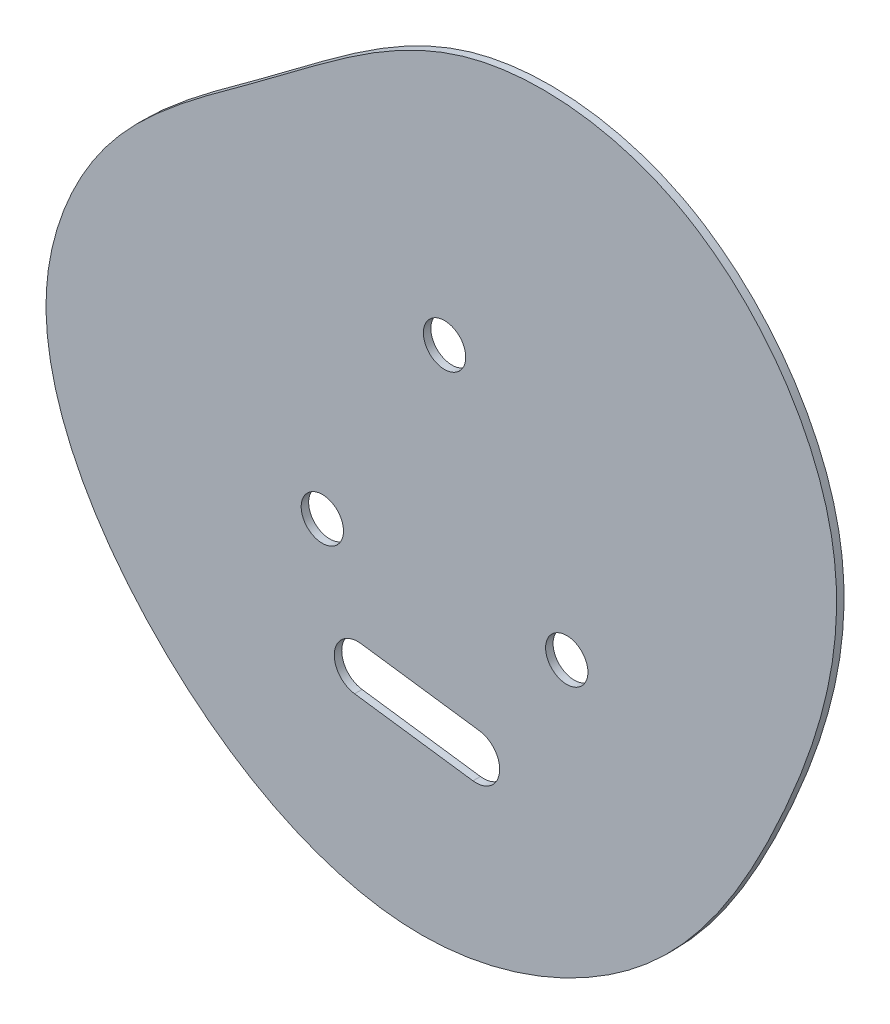
SolidWorks part; units mm, degrees
ref_plane "Front Plane" through (0, 0, 0) normal (0, 0, 1) x (1, 0, 0)
ref_plane "Top Plane" through (0, 0, 0) normal (0, 1, 0) x (1, 0, 0)
ref_plane "Right Plane" through (0, 0, 0) normal (1, 0, 0) x (0, 0, -1)
curve "Curve1"
sketch "Sketch1" plane through (0, 0, 0) normal (0, 0, 1) x (1, 0, 0)
  line L0 (20.4693, 0) -> (28.509, 1.873) construction
  line L1 (-7.4885, 18.6017) -> (-9.9714, 26.4745) construction
  line L2 (8.0513, 16.8361) -> (11.9387, 24.1185) construction
  line L3 (-27.2349, 6.6205) -> (-31.7687, 13.5191) construction
  line L5 (-46.6878, -17.9332) -> (-54.9428, -17.9332) construction
  line L6 (-36.9963, -38.0282) -> (-42.9348, -43.7622) construction
  line L7 (-15.1134, -48.5484) -> (-15.1134, -56.8034) construction
  line L8 (3.1727, -41.5248) -> (8.5042, -47.8272) construction
  line L9 (15.4652, -23.8475) -> (23.0712, -27.056) construction
  line L10 (-42.2751, -6.3732) -> (-48.8404, -1.369) construction
  spline S0 degree 3 poles (20.4719, -0.3582) (20.4906, 0.0056) (20.3791, 0.3547) (20.2968, 0.7085) (20.2014, 1.0583) (20.1045, 1.4055) (20.003, 1.7496) (19.8979, 2.091) (19.7889, 2.4294) (19.6761, 2.7649) (19.5596, 3.0976) (19.4394, 3.4274) (19.3156, 3.7542) (19.1882, 4.0783) (19.0573, 4.3994) (18.9228, 4.7177) (18.7848, 5.0331) (18.6433, 5.3456) (18.4984, 5.6553) (18.3501, 5.962) (18.1985, 6.266) (18.0434, 6.567) (17.8851, 6.8652) (17.7235, 7.1605) (17.5586, 7.4529) (17.3904, 7.7425) (17.219, 8.0291) (17.0444, 8.3129) (16.8666, 8.5937) (16.6856, 8.8717) (16.5014, 9.1467) (16.3141, 9.4188) (16.1237, 9.6879) (15.9302, 9.9541) (15.7336, 10.2173) (15.5338, 10.4776) (15.3311, 10.7348) (15.1252, 10.989) (14.9164, 11.2402) (14.7045, 11.4883) (14.4895, 11.7333) (14.2716, 11.9752) (14.0507, 12.214) (13.8268, 12.4496) (13.5999, 12.6821) (13.3701, 12.9113) (13.1374, 13.1373) (12.9017, 13.3601) (12.6631, 13.5795) (12.4217, 13.7956) (12.1773, 14.0084) (11.9301, 14.2177) (11.68, 14.4236) (11.4271, 14.626) (11.1713, 14.8249) (10.9128, 15.0202) (10.6515, 15.212) (10.3875, 15.4001) (10.1207, 15.5845) (9.8512, 15.7652) (9.579, 15.9422) (9.3041, 16.1153) (9.0266, 16.2845) (8.7465, 16.4499) (8.4638, 16.6112) (8.1785, 16.7686) (7.8907, 16.9219) (7.6005, 17.0711) (7.3077, 17.2161) (7.0126, 17.357) (6.715, 17.4935) (6.4152, 17.6257) (6.113, 17.7536) (5.8085, 17.877) (5.5018, 17.996) (5.193, 18.1104) (4.882, 18.2202) (4.5689, 18.3254) (4.2539, 18.4259) (3.9368, 18.5217) (3.6178, 18.6126) (3.297, 18.6987) (2.9743, 18.7798) (2.6499, 18.856) (2.3239, 18.9272) (1.9962, 18.9933) (1.6669, 19.0543) (1.3362, 19.11) (1.0041, 19.1606) (0.6706, 19.2059) (0.3358, 19.2458) (-0.0001, 19.2804) (-0.3372, 19.3095) (-0.6752, 19.3332) (-1.0143, 19.3513) (-1.3542, 19.3639) (-1.6948, 19.3709) (-2.0362, 19.3722) (-2.3782, 19.3678) (-2.7207, 19.3577) (-3.0636, 19.3418) (-3.4068, 19.3201) (-3.7502, 19.2926) (-4.0938, 19.2592) (-4.4374, 19.2198) (-4.7809, 19.1746) (-5.1242, 19.1233) (-5.4672, 19.0661) (-5.8099, 19.0029) (-6.152, 18.9336) (-6.4935, 18.8583) (-6.8343, 18.7768) (-7.1743, 18.6893) (-7.5133, 18.5957) (-7.8512, 18.496) (-8.1879, 18.3901) (-8.5233, 18.2781) (-8.8573, 18.16) (-9.1898, 18.0358) (-9.5206, 17.9054) (-9.8496, 17.7689) (-10.1766, 17.6262) (-10.5017, 17.4775) (-10.8245, 17.3227) (-11.1451, 17.1617) (-11.4632, 16.9947) (-11.7791, 16.822) (-12.0927, 16.6439) (-12.4044, 16.4609) (-12.7144, 16.2733) (-13.0229, 16.0815) (-13.3301, 15.8857) (-13.6364, 15.6864) (-13.9422, 15.4837) (-14.2476, 15.278) (-14.5531, 15.0694) (-14.859, 14.8581) (-15.1658, 14.6444) (-15.4738, 14.4285) (-15.7835, 14.2103) (-16.0953, 13.99) (-16.4096, 13.7678) (-16.7269, 13.5435) (-17.0477, 13.3173) (-17.3725, 13.0891) (-17.7016, 12.8589) (-18.0357, 12.6265) (-18.3753, 12.3918) (-18.7207, 12.1548) (-19.0726, 11.9151) (-19.4314, 11.6726) (-19.7976, 11.4271) (-20.1718, 11.1782) (-20.5544, 10.9256) (-20.9459, 10.669) (-21.3468, 10.4079) (-21.7576, 10.142) (-22.1787, 9.8708) (-22.6107, 9.5937) (-23.0538, 9.3103) (-23.5087, 9.0201) (-23.9757, 8.7223) (-24.4552, 8.4163) (-24.9476, 8.1016) (-25.4532, 7.7775) (-25.9724, 7.443) (-26.5055, 7.0977) (-27.0528, 6.7405) (-27.6146, 6.3708) (-28.1911, 5.9877) (-28.7826, 5.5902) (-29.3891, 5.1775) (-30.011, 4.7487) (-30.6482, 4.3027) (-31.3009, 3.8387) (-31.9692, 3.3555) (-32.6531, 2.8522) (-33.3524, 2.3277) (-34.0663, 1.7816) (-34.7922, 1.212) (-35.5264, 0.6179) (-36.2656, -0.0015) (-37.006, -0.6467) (-37.7441, -1.3181) (-38.4762, -2.0158) (-39.1988, -2.7397) (-39.9081, -3.4895) (-40.6005, -4.2646) (-41.2726, -5.0643) (-41.9207, -5.8876) (-42.5414, -6.7333) (-43.1312, -7.6) (-43.6867, -8.4861) (-44.2047, -9.3896) (-44.6819, -10.3087) (-45.1152, -11.2411) (-45.5015, -12.1842) (-45.838, -13.1356) (-46.1218, -14.0922) (-46.3502, -15.0514) (-46.5207, -16.0105) (-46.6353, -16.9668) (-46.6959, -17.9187) (-46.7048, -18.8646) (-46.6641, -19.8031) (-46.576, -20.7331) (-46.4429, -21.6534) (-46.2667, -22.5631) (-46.0499, -23.4614) (-45.7945, -24.3476) (-45.5028, -25.2212) (-45.1769, -26.0818) (-44.8189, -26.9291) (-44.431, -27.763) (-44.0152, -28.5834) (-43.5736, -29.3905) (-43.1082, -30.1845) (-42.6208, -30.9657) (-42.1134, -31.7347) (-41.5877, -32.4919) (-41.0455, -33.2381) (-40.4886, -33.9741) (-39.9184, -34.7007) (-39.3348, -35.4173) (-38.7375, -36.1234) (-38.1264, -36.8183) (-37.5012, -37.5012) (-36.8618, -38.1715) (-36.2081, -38.8285) (-35.5401, -39.4713) (-34.8578, -40.0993) (-34.1611, -40.7116) (-33.4502, -41.3075) (-32.725, -41.8861) (-31.9858, -42.4467) (-31.2328, -42.9883) (-30.4661, -43.5102) (-29.686, -44.0114) (-28.8928, -44.4912) (-28.0869, -44.9487) (-27.2687, -45.383) (-26.4385, -45.7933) (-25.5969, -46.1786) (-24.7444, -46.5382) (-23.8816, -46.8712) (-23.009, -47.1767) (-22.1274, -47.454) (-21.2375, -47.7021) (-20.34, -47.9203) (-19.4357, -48.1077) (-18.5254, -48.2636) (-17.6101, -48.3873) (-16.6907, -48.4779) (-15.7681, -48.5348) (-14.8434, -48.5572) (-13.9176, -48.5444) (-12.9919, -48.4959) (-12.0676, -48.4109) (-11.1461, -48.29) (-10.2287, -48.1341) (-9.3169, -47.9441) (-8.412, -47.7209) (-7.5154, -47.4656) (-6.6283, -47.1791) (-5.7518, -46.8626) (-4.887, -46.5172) (-4.035, -46.144) (-3.1968, -45.7443) (-2.3733, -45.3192) (-1.5652, -44.87) (-0.7734, -44.398) (0.0014, -43.9045) (0.7587, -43.3908) (1.4978, -42.8582) (2.2183, -42.3081) (2.9197, -41.7419) (3.6018, -41.1608) (4.2642, -40.5664) (4.9068, -39.9599) (5.5294, -39.3427) (6.132, -38.7162) (6.7146, -38.0817) (7.2773, -37.4407) (7.8203, -36.7944) (8.3437, -36.1442) (8.8479, -35.4914) (9.3333, -34.8372) (9.8003, -34.183) (10.2494, -33.5299) (10.6811, -32.8793) (11.0962, -32.2321) (11.4952, -31.5897) (11.8791, -30.953) (12.2485, -30.3226) (12.6037, -29.6986) (12.9452, -29.0811) (13.2733, -28.4704) (13.5887, -27.8663) (13.8917, -27.2691) (14.1827, -26.6788) (14.4623, -26.0953) (14.7307, -25.5188) (14.9884, -24.9492) (15.2358, -24.3866) (15.4733, -23.8309) (15.7014, -23.2821) (15.9202, -22.7402) (16.1303, -22.2051) (16.332, -21.6768) (16.5257, -21.1552) (16.7115, -20.6403) (16.89, -20.1319) (17.0614, -19.63) (17.2261, -19.1344) (17.3842, -18.6451) (17.5361, -18.1619) (17.6822, -17.6848) (17.8225, -17.2135) (17.9574, -16.748) (18.0872, -16.2881) (18.2121, -15.8337) (18.3322, -15.3847) (18.4478, -14.9408) (18.5591, -14.5019) (18.6662, -14.0679) (18.7694, -13.6386) (18.8688, -13.2138) (18.9646, -12.7934) (19.0568, -12.3772) (19.1457, -11.9651) (19.2313, -11.5568) (19.3138, -11.1522) (19.3933, -10.7511) (19.4697, -10.3534) (19.5433, -9.959) (19.6141, -9.5675) (19.6821, -9.1789) (19.7474, -8.7931) (19.8101, -8.4098) (19.87, -8.0288) (19.9274, -7.6502) (19.9821, -7.2736) (20.0342, -6.899) (20.0836, -6.5262) (20.1304, -6.1551) (20.1746, -5.7855) (20.216, -5.4173) (20.2547, -5.0505) (20.2905, -4.6848) (20.3236, -4.3203) (20.3537, -3.9567) (20.3809, -3.594) (20.4049, -3.2321) (20.4259, -2.8709) (20.4437, -2.5104) (20.4581, -2.1504) (20.4692, -1.791) (20.4769, -1.432) (20.4803, -1.0735) (20.4824, -0.7151) (20.4719, -0.3582) (20.4906, 0.0056) (20.3791, 0.3547) knots -0.005175 -0.003449 -0.001724 0 0.001764 0.003519 0.005266 0.007004 0.008734 0.010456 0.01217 0.013877 0.015576 0.017268 0.018953 0.020632 0.022304 0.02397 0.02563 0.027283 0.028932 0.030575 0.032212 0.033845 0.035472 0.037095 0.038714 0.040328 0.041938 0.043545 0.045147 0.046746 0.048342 0.049935 0.051524 0.053111 0.054695 0.056276 0.057855 0.059432 0.061007 0.06258 0.064152 0.065721 0.06729 0.068857 0.070423 0.071988 0.073552 0.075115 0.076678 0.07824 0.079802 0.081364 0.082926 0.084488 0.08605 0.087612 0.089174 0.090737 0.092301 0.093865 0.095431 0.096997 0.098564 0.100132 0.101701 0.103272 0.104844 0.106418 0.107993 0.109569 0.111148 0.112728 0.11431 0.115894 0.117479 0.119067 0.120657 0.12225 0.123844 0.125441 0.12704 0.128642 0.130246 0.131852 0.133461 0.135073 0.136687 0.138304 0.139924 0.141547 0.143172 0.1448 0.146431 0.148065 0.149702 0.151342 0.152985 0.154631 0.156279 0.157931 0.159586 0.161244 0.162905 0.16457 0.166237 0.167907 0.169581 0.171258 0.172937 0.17462 0.176307 0.177996 0.179688 0.181384 0.183082 0.184784 0.186489 0.188197 0.189908 0.191622 0.19334 0.19506 0.196783 0.19851 0.200239 0.201971 0.203707 0.205446 0.207188 0.208935 0.210686 0.212442 0.214204 0.215972 0.217748 0.219531 0.221323 0.223125 0.224939 0.226765 0.228604 0.23046 0.232333 0.234225 0.236138 0.238074 0.240035 0.242024 0.244043 0.246095 0.248182 0.250307 0.252473 0.254682 0.256938 0.259244 0.261602 0.264016 0.26649 0.269025 0.271625 0.274295 0.277036 0.279852 0.282747 0.285724 0.288785 0.291935 0.295176 0.298513 0.301947 0.305484 0.309124 0.312873 0.316734 0.320709 0.324801 0.329015 0.333352 0.337803 0.34236 0.347013 0.351751 0.356565 0.361444 0.366378 0.371357 0.376371 0.38141 0.386464 0.391524 0.39658 0.401624 0.406647 0.411641 0.416599 0.421513 0.426378 0.431188 0.43594 0.440632 0.445271 0.449865 0.454421 0.458946 0.463447 0.467927 0.472391 0.476844 0.481289 0.485727 0.490163 0.494596 0.499029 0.503463 0.507898 0.512334 0.516773 0.521215 0.525659 0.530106 0.534555 0.539008 0.543464 0.547923 0.552384 0.556848 0.561315 0.565783 0.570252 0.574723 0.579195 0.583667 0.588139 0.592612 0.597084 0.601555 0.606025 0.610494 0.614962 0.619428 0.623892 0.628354 0.632814 0.637273 0.641729 0.646184 0.650638 0.65509 0.659542 0.663994 0.668446 0.672899 0.677354 0.681812 0.686275 0.690742 0.695217 0.699697 0.704183 0.708673 0.713166 0.717661 0.722155 0.726648 0.731137 0.735622 0.740099 0.744568 0.749025 0.75347 0.757899 0.762311 0.766703 0.771074 0.775421 0.779741 0.784033 0.788293 0.792521 0.796712 0.800866 0.804979 0.809049 0.813074 0.817052 0.82098 0.824856 0.828677 0.832443 0.83615 0.839797 0.843382 0.846904 0.850365 0.853767 0.857109 0.860394 0.863623 0.866796 0.869914 0.87298 0.875994 0.878957 0.88187 0.884735 0.887552 0.890324 0.89305 0.895732 0.898371 0.900968 0.903525 0.906043 0.908522 0.910963 0.913369 0.915739 0.918076 0.920379 0.922651 0.924892 0.927103 0.929285 0.93144 0.933569 0.935672 0.93775 0.939805 0.941838 0.943849 0.94584 0.94781 0.949763 0.951697 0.953615 0.955517 0.957403 0.959276 0.961134 0.962981 0.964815 0.966638 0.968451 0.970255 0.972049 0.973835 0.975613 0.977385 0.979149 0.980908 0.982662 0.98441 0.986154 0.987894 0.989631 0.991365 0.993096 0.994825 0.996551 0.998276 1 1.001764 1.003519 1.005266 only from (20.4693, 0) to (20.4693, 0) construction
  spline S1 degree 3 poles (20.4719, -0.3582) (20.4906, 0.0056) (20.3791, 0.3547) (20.2968, 0.7085) (20.2014, 1.0583) (20.1045, 1.4055) (20.003, 1.7496) (19.8979, 2.091) (19.7889, 2.4294) (19.6761, 2.7649) (19.5596, 3.0976) (19.4394, 3.4274) (19.3156, 3.7542) (19.1882, 4.0783) (19.0573, 4.3994) (18.9228, 4.7177) (18.7848, 5.0331) (18.6433, 5.3456) (18.4984, 5.6553) (18.3501, 5.962) (18.1985, 6.266) (18.0434, 6.567) (17.8851, 6.8652) (17.7235, 7.1605) (17.5586, 7.4529) (17.3904, 7.7425) (17.219, 8.0291) (17.0444, 8.3129) (16.8666, 8.5937) (16.6856, 8.8717) (16.5014, 9.1467) (16.3141, 9.4188) (16.1237, 9.6879) (15.9302, 9.9541) (15.7336, 10.2173) (15.5338, 10.4776) (15.3311, 10.7348) (15.1252, 10.989) (14.9164, 11.2402) (14.7045, 11.4883) (14.4895, 11.7333) (14.2716, 11.9752) (14.0507, 12.214) (13.8268, 12.4496) (13.5999, 12.6821) (13.3701, 12.9113) (13.1374, 13.1373) (12.9017, 13.3601) (12.6631, 13.5795) (12.4217, 13.7956) (12.1773, 14.0084) (11.9301, 14.2177) (11.68, 14.4236) (11.4271, 14.626) (11.1713, 14.8249) (10.9128, 15.0202) (10.6515, 15.212) (10.3875, 15.4001) (10.1207, 15.5845) (9.8512, 15.7652) (9.579, 15.9422) (9.3041, 16.1153) (9.0266, 16.2845) (8.7465, 16.4499) (8.4638, 16.6112) (8.1785, 16.7686) (7.8907, 16.9219) (7.6005, 17.0711) (7.3077, 17.2161) (7.0126, 17.357) (6.715, 17.4935) (6.4152, 17.6257) (6.113, 17.7536) (5.8085, 17.877) (5.5018, 17.996) (5.193, 18.1104) (4.882, 18.2202) (4.5689, 18.3254) (4.2539, 18.4259) (3.9368, 18.5217) (3.6178, 18.6126) (3.297, 18.6987) (2.9743, 18.7798) (2.6499, 18.856) (2.3239, 18.9272) (1.9962, 18.9933) (1.6669, 19.0543) (1.3362, 19.11) (1.0041, 19.1606) (0.6706, 19.2059) (0.3358, 19.2458) (-0.0001, 19.2804) (-0.3372, 19.3095) (-0.6752, 19.3332) (-1.0143, 19.3513) (-1.3542, 19.3639) (-1.6948, 19.3709) (-2.0362, 19.3722) (-2.3782, 19.3678) (-2.7207, 19.3577) (-3.0636, 19.3418) (-3.4068, 19.3201) (-3.7502, 19.2926) (-4.0938, 19.2592) (-4.4374, 19.2198) (-4.7809, 19.1746) (-5.1242, 19.1233) (-5.4672, 19.0661) (-5.8099, 19.0029) (-6.152, 18.9336) (-6.4935, 18.8583) (-6.8343, 18.7768) (-7.1743, 18.6893) (-7.5133, 18.5957) (-7.8512, 18.496) (-8.1879, 18.3901) (-8.5233, 18.2781) (-8.8573, 18.16) (-9.1898, 18.0358) (-9.5206, 17.9054) (-9.8496, 17.7689) (-10.1766, 17.6262) (-10.5017, 17.4775) (-10.8245, 17.3227) (-11.1451, 17.1617) (-11.4632, 16.9947) (-11.7791, 16.822) (-12.0927, 16.6439) (-12.4044, 16.4609) (-12.7144, 16.2733) (-13.0229, 16.0815) (-13.3301, 15.8857) (-13.6364, 15.6864) (-13.9422, 15.4837) (-14.2476, 15.278) (-14.5531, 15.0694) (-14.859, 14.8581) (-15.1658, 14.6444) (-15.4738, 14.4285) (-15.7835, 14.2103) (-16.0953, 13.99) (-16.4096, 13.7678) (-16.7269, 13.5435) (-17.0477, 13.3173) (-17.3725, 13.0891) (-17.7016, 12.8589) (-18.0357, 12.6265) (-18.3753, 12.3918) (-18.7207, 12.1548) (-19.0726, 11.9151) (-19.4314, 11.6726) (-19.7976, 11.4271) (-20.1718, 11.1782) (-20.5544, 10.9256) (-20.9459, 10.669) (-21.3468, 10.4079) (-21.7576, 10.142) (-22.1787, 9.8708) (-22.6107, 9.5937) (-23.0538, 9.3103) (-23.5087, 9.0201) (-23.9757, 8.7223) (-24.4552, 8.4163) (-24.9476, 8.1016) (-25.4532, 7.7775) (-25.9724, 7.443) (-26.5055, 7.0977) (-27.0528, 6.7405) (-27.6146, 6.3708) (-28.1911, 5.9877) (-28.7826, 5.5902) (-29.3891, 5.1775) (-30.011, 4.7487) (-30.6482, 4.3027) (-31.3009, 3.8387) (-31.9692, 3.3555) (-32.6531, 2.8522) (-33.3524, 2.3277) (-34.0663, 1.7816) (-34.7922, 1.212) (-35.5264, 0.6179) (-36.2656, -0.0015) (-37.006, -0.6467) (-37.7441, -1.3181) (-38.4762, -2.0158) (-39.1988, -2.7397) (-39.9081, -3.4895) (-40.6005, -4.2646) (-41.2726, -5.0643) (-41.9207, -5.8876) (-42.5414, -6.7333) (-43.1312, -7.6) (-43.6867, -8.4861) (-44.2047, -9.3896) (-44.6819, -10.3087) (-45.1152, -11.2411) (-45.5015, -12.1842) (-45.838, -13.1356) (-46.1218, -14.0922) (-46.3502, -15.0514) (-46.5207, -16.0105) (-46.6353, -16.9668) (-46.6959, -17.9187) (-46.7048, -18.8646) (-46.6641, -19.8031) (-46.576, -20.7331) (-46.4429, -21.6534) (-46.2667, -22.5631) (-46.0499, -23.4614) (-45.7945, -24.3476) (-45.5028, -25.2212) (-45.1769, -26.0818) (-44.8189, -26.9291) (-44.431, -27.763) (-44.0152, -28.5834) (-43.5736, -29.3905) (-43.1082, -30.1845) (-42.6208, -30.9657) (-42.1134, -31.7347) (-41.5877, -32.4919) (-41.0455, -33.2381) (-40.4886, -33.9741) (-39.9184, -34.7007) (-39.3348, -35.4173) (-38.7375, -36.1234) (-38.1264, -36.8183) (-37.5012, -37.5012) (-36.8618, -38.1715) (-36.2081, -38.8285) (-35.5401, -39.4713) (-34.8578, -40.0993) (-34.1611, -40.7116) (-33.4502, -41.3075) (-32.725, -41.8861) (-31.9858, -42.4467) (-31.2328, -42.9883) (-30.4661, -43.5102) (-29.686, -44.0114) (-28.8928, -44.4912) (-28.0869, -44.9487) (-27.2687, -45.383) (-26.4385, -45.7933) (-25.5969, -46.1786) (-24.7444, -46.5382) (-23.8816, -46.8712) (-23.009, -47.1767) (-22.1274, -47.454) (-21.2375, -47.7021) (-20.34, -47.9203) (-19.4357, -48.1077) (-18.5254, -48.2636) (-17.6101, -48.3873) (-16.6907, -48.4779) (-15.7681, -48.5348) (-14.8434, -48.5572) (-13.9176, -48.5444) (-12.9919, -48.4959) (-12.0676, -48.4109) (-11.1461, -48.29) (-10.2287, -48.1341) (-9.3169, -47.9441) (-8.412, -47.7209) (-7.5154, -47.4656) (-6.6283, -47.1791) (-5.7518, -46.8626) (-4.887, -46.5172) (-4.035, -46.144) (-3.1968, -45.7443) (-2.3733, -45.3192) (-1.5652, -44.87) (-0.7734, -44.398) (0.0014, -43.9045) (0.7587, -43.3908) (1.4978, -42.8582) (2.2183, -42.3081) (2.9197, -41.7419) (3.6018, -41.1608) (4.2642, -40.5664) (4.9068, -39.9599) (5.5294, -39.3427) (6.132, -38.7162) (6.7146, -38.0817) (7.2773, -37.4407) (7.8203, -36.7944) (8.3437, -36.1442) (8.8479, -35.4914) (9.3333, -34.8372) (9.8003, -34.183) (10.2494, -33.5299) (10.6811, -32.8793) (11.0962, -32.2321) (11.4952, -31.5897) (11.8791, -30.953) (12.2485, -30.3226) (12.6037, -29.6986) (12.9452, -29.0811) (13.2733, -28.4704) (13.5887, -27.8663) (13.8917, -27.2691) (14.1827, -26.6788) (14.4623, -26.0953) (14.7307, -25.5188) (14.9884, -24.9492) (15.2358, -24.3866) (15.4733, -23.8309) (15.7014, -23.2821) (15.9202, -22.7402) (16.1303, -22.2051) (16.332, -21.6768) (16.5257, -21.1552) (16.7115, -20.6403) (16.89, -20.1319) (17.0614, -19.63) (17.2261, -19.1344) (17.3842, -18.6451) (17.5361, -18.1619) (17.6822, -17.6848) (17.8225, -17.2135) (17.9574, -16.748) (18.0872, -16.2881) (18.2121, -15.8337) (18.3322, -15.3847) (18.4478, -14.9408) (18.5591, -14.5019) (18.6662, -14.0679) (18.7694, -13.6386) (18.8688, -13.2138) (18.9646, -12.7934) (19.0568, -12.3772) (19.1457, -11.9651) (19.2313, -11.5568) (19.3138, -11.1522) (19.3933, -10.7511) (19.4697, -10.3534) (19.5433, -9.959) (19.6141, -9.5675) (19.6821, -9.1789) (19.7474, -8.7931) (19.8101, -8.4098) (19.87, -8.0288) (19.9274, -7.6502) (19.9821, -7.2736) (20.0342, -6.899) (20.0836, -6.5262) (20.1304, -6.1551) (20.1746, -5.7855) (20.216, -5.4173) (20.2547, -5.0505) (20.2905, -4.6848) (20.3236, -4.3203) (20.3537, -3.9567) (20.3809, -3.594) (20.4049, -3.2321) (20.4259, -2.8709) (20.4437, -2.5104) (20.4581, -2.1504) (20.4692, -1.791) (20.4769, -1.432) (20.4803, -1.0735) (20.4824, -0.7151) (20.4719, -0.3582) (20.4906, 0.0056) (20.3791, 0.3547) knots -0.005175 -0.003449 -0.001724 0 0.001764 0.003519 0.005266 0.007004 0.008734 0.010456 0.01217 0.013877 0.015576 0.017268 0.018953 0.020632 0.022304 0.02397 0.02563 0.027283 0.028932 0.030575 0.032212 0.033845 0.035472 0.037095 0.038714 0.040328 0.041938 0.043545 0.045147 0.046746 0.048342 0.049935 0.051524 0.053111 0.054695 0.056276 0.057855 0.059432 0.061007 0.06258 0.064152 0.065721 0.06729 0.068857 0.070423 0.071988 0.073552 0.075115 0.076678 0.07824 0.079802 0.081364 0.082926 0.084488 0.08605 0.087612 0.089174 0.090737 0.092301 0.093865 0.095431 0.096997 0.098564 0.100132 0.101701 0.103272 0.104844 0.106418 0.107993 0.109569 0.111148 0.112728 0.11431 0.115894 0.117479 0.119067 0.120657 0.12225 0.123844 0.125441 0.12704 0.128642 0.130246 0.131852 0.133461 0.135073 0.136687 0.138304 0.139924 0.141547 0.143172 0.1448 0.146431 0.148065 0.149702 0.151342 0.152985 0.154631 0.156279 0.157931 0.159586 0.161244 0.162905 0.16457 0.166237 0.167907 0.169581 0.171258 0.172937 0.17462 0.176307 0.177996 0.179688 0.181384 0.183082 0.184784 0.186489 0.188197 0.189908 0.191622 0.19334 0.19506 0.196783 0.19851 0.200239 0.201971 0.203707 0.205446 0.207188 0.208935 0.210686 0.212442 0.214204 0.215972 0.217748 0.219531 0.221323 0.223125 0.224939 0.226765 0.228604 0.23046 0.232333 0.234225 0.236138 0.238074 0.240035 0.242024 0.244043 0.246095 0.248182 0.250307 0.252473 0.254682 0.256938 0.259244 0.261602 0.264016 0.26649 0.269025 0.271625 0.274295 0.277036 0.279852 0.282747 0.285724 0.288785 0.291935 0.295176 0.298513 0.301947 0.305484 0.309124 0.312873 0.316734 0.320709 0.324801 0.329015 0.333352 0.337803 0.34236 0.347013 0.351751 0.356565 0.361444 0.366378 0.371357 0.376371 0.38141 0.386464 0.391524 0.39658 0.401624 0.406647 0.411641 0.416599 0.421513 0.426378 0.431188 0.43594 0.440632 0.445271 0.449865 0.454421 0.458946 0.463447 0.467927 0.472391 0.476844 0.481289 0.485727 0.490163 0.494596 0.499029 0.503463 0.507898 0.512334 0.516773 0.521215 0.525659 0.530106 0.534555 0.539008 0.543464 0.547923 0.552384 0.556848 0.561315 0.565783 0.570252 0.574723 0.579195 0.583667 0.588139 0.592612 0.597084 0.601555 0.606025 0.610494 0.614962 0.619428 0.623892 0.628354 0.632814 0.637273 0.641729 0.646184 0.650638 0.65509 0.659542 0.663994 0.668446 0.672899 0.677354 0.681812 0.686275 0.690742 0.695217 0.699697 0.704183 0.708673 0.713166 0.717661 0.722155 0.726648 0.731137 0.735622 0.740099 0.744568 0.749025 0.75347 0.757899 0.762311 0.766703 0.771074 0.775421 0.779741 0.784033 0.788293 0.792521 0.796712 0.800866 0.804979 0.809049 0.813074 0.817052 0.82098 0.824856 0.828677 0.832443 0.83615 0.839797 0.843382 0.846904 0.850365 0.853767 0.857109 0.860394 0.863623 0.866796 0.869914 0.87298 0.875994 0.878957 0.88187 0.884735 0.887552 0.890324 0.89305 0.895732 0.898371 0.900968 0.903525 0.906043 0.908522 0.910963 0.913369 0.915739 0.918076 0.920379 0.922651 0.924892 0.927103 0.929285 0.93144 0.933569 0.935672 0.93775 0.939805 0.941838 0.943849 0.94584 0.94781 0.949763 0.951697 0.953615 0.955517 0.957403 0.959276 0.961134 0.962981 0.964815 0.966638 0.968451 0.970255 0.972049 0.973835 0.975613 0.977385 0.979149 0.980908 0.982662 0.98441 0.986154 0.987894 0.989631 0.991365 0.993096 0.994825 0.996551 0.998276 1 1.001764 1.003519 1.005266 only from (20.4693, 0) to (20.4693, 0) construction
  spline S2 degree 3 poles (33.3871, 1.6837) (15.4174, 26.6729) (-12.247, 29.2168) (-30.8395, 13.6102) (-49.3035, 1.4886) (-58.5486, -21.6644) (-44.4112, -46.5615) (-17.2285, -61.1449) (10.6799, -49.6929) (24.5537, -26.4797) (33.3871, 1.6837) (15.4174, 26.6729) (-12.247, 29.2168) knots -0.324063 -0.224462 -0.1089 0 0.086513 0.186061 0.27499 0.344292 0.456117 0.576746 0.675937 0.775538 0.8911 1 1.086513 1.186061 1.27499 only from (11.9387, 24.1185) to (11.9387, 24.1185)
  dimension "D1" = 8.255
extrude "Boss-Extrude1" add sketch "Sketch1" along normal mid plane 0.7937
sketch "Sketch4" plane through (0, 0, 0.3969) normal (0, 0, 1) x (1, 0, 0)
  line L0 (17.7659, -20.9602) -> (-1.4085, -53.5016) construction
  line L1 (-50.4616, -14.4148) -> (-15.5658, 21.7389) construction
  circle A0 centre (-12.5939, -16.2726) radius 28.5365 construction
  spline S1 degree 3 poles (20.4719, -0.3582) (20.4906, 0.0056) (20.3791, 0.3547) (20.2968, 0.7085) (20.2014, 1.0583) (20.1045, 1.4055) (20.003, 1.7496) (19.8979, 2.091) (19.7889, 2.4294) (19.6761, 2.7649) (19.5596, 3.0976) (19.4394, 3.4274) (19.3156, 3.7542) (19.1882, 4.0783) (19.0573, 4.3994) (18.9228, 4.7177) (18.7848, 5.0331) (18.6433, 5.3456) (18.4984, 5.6553) (18.3501, 5.962) (18.1985, 6.266) (18.0434, 6.567) (17.8851, 6.8652) (17.7235, 7.1605) (17.5586, 7.4529) (17.3904, 7.7425) (17.219, 8.0291) (17.0444, 8.3129) (16.8666, 8.5937) (16.6856, 8.8717) (16.5014, 9.1467) (16.3141, 9.4188) (16.1237, 9.6879) (15.9302, 9.9541) (15.7336, 10.2173) (15.5338, 10.4776) (15.3311, 10.7348) (15.1252, 10.989) (14.9164, 11.2402) (14.7045, 11.4883) (14.4895, 11.7333) (14.2716, 11.9752) (14.0507, 12.214) (13.8268, 12.4496) (13.5999, 12.6821) (13.3701, 12.9113) (13.1374, 13.1373) (12.9017, 13.3601) (12.6631, 13.5795) (12.4217, 13.7956) (12.1773, 14.0084) (11.9301, 14.2177) (11.68, 14.4236) (11.4271, 14.626) (11.1713, 14.8249) (10.9128, 15.0202) (10.6515, 15.212) (10.3875, 15.4001) (10.1207, 15.5845) (9.8512, 15.7652) (9.579, 15.9422) (9.3041, 16.1153) (9.0266, 16.2845) (8.7465, 16.4499) (8.4638, 16.6112) (8.1785, 16.7686) (7.8907, 16.9219) (7.6005, 17.0711) (7.3077, 17.2161) (7.0126, 17.357) (6.715, 17.4935) (6.4152, 17.6257) (6.113, 17.7536) (5.8085, 17.877) (5.5018, 17.996) (5.193, 18.1104) (4.882, 18.2202) (4.5689, 18.3254) (4.2539, 18.4259) (3.9368, 18.5217) (3.6178, 18.6126) (3.297, 18.6987) (2.9743, 18.7798) (2.6499, 18.856) (2.3239, 18.9272) (1.9962, 18.9933) (1.6669, 19.0543) (1.3362, 19.11) (1.0041, 19.1606) (0.6706, 19.2059) (0.3358, 19.2458) (-0.0001, 19.2804) (-0.3372, 19.3095) (-0.6752, 19.3332) (-1.0143, 19.3513) (-1.3542, 19.3639) (-1.6948, 19.3709) (-2.0362, 19.3722) (-2.3782, 19.3678) (-2.7207, 19.3577) (-3.0636, 19.3418) (-3.4068, 19.3201) (-3.7502, 19.2926) (-4.0938, 19.2592) (-4.4374, 19.2198) (-4.7809, 19.1746) (-5.1242, 19.1233) (-5.4672, 19.0661) (-5.8099, 19.0029) (-6.152, 18.9336) (-6.4935, 18.8583) (-6.8343, 18.7768) (-7.1743, 18.6893) (-7.5133, 18.5957) (-7.8512, 18.496) (-8.1879, 18.3901) (-8.5233, 18.2781) (-8.8573, 18.16) (-9.1898, 18.0358) (-9.5206, 17.9054) (-9.8496, 17.7689) (-10.1766, 17.6262) (-10.5017, 17.4775) (-10.8245, 17.3227) (-11.1451, 17.1617) (-11.4632, 16.9947) (-11.7791, 16.822) (-12.0927, 16.6439) (-12.4044, 16.4609) (-12.7144, 16.2733) (-13.0229, 16.0815) (-13.3301, 15.8857) (-13.6364, 15.6864) (-13.9422, 15.4837) (-14.2476, 15.278) (-14.5531, 15.0694) (-14.859, 14.8581) (-15.1658, 14.6444) (-15.4738, 14.4285) (-15.7835, 14.2103) (-16.0953, 13.99) (-16.4096, 13.7678) (-16.7269, 13.5435) (-17.0477, 13.3173) (-17.3725, 13.0891) (-17.7016, 12.8589) (-18.0357, 12.6265) (-18.3753, 12.3918) (-18.7207, 12.1548) (-19.0726, 11.9151) (-19.4314, 11.6726) (-19.7976, 11.4271) (-20.1718, 11.1782) (-20.5544, 10.9256) (-20.9459, 10.669) (-21.3468, 10.4079) (-21.7576, 10.142) (-22.1787, 9.8708) (-22.6107, 9.5937) (-23.0538, 9.3103) (-23.5087, 9.0201) (-23.9757, 8.7223) (-24.4552, 8.4163) (-24.9476, 8.1016) (-25.4532, 7.7775) (-25.9724, 7.443) (-26.5055, 7.0977) (-27.0528, 6.7405) (-27.6146, 6.3708) (-28.1911, 5.9877) (-28.7826, 5.5902) (-29.3891, 5.1775) (-30.011, 4.7487) (-30.6482, 4.3027) (-31.3009, 3.8387) (-31.9692, 3.3555) (-32.6531, 2.8522) (-33.3524, 2.3277) (-34.0663, 1.7816) (-34.7922, 1.212) (-35.5264, 0.6179) (-36.2656, -0.0015) (-37.006, -0.6467) (-37.7441, -1.3181) (-38.4762, -2.0158) (-39.1988, -2.7397) (-39.9081, -3.4895) (-40.6005, -4.2646) (-41.2726, -5.0643) (-41.9207, -5.8876) (-42.5414, -6.7333) (-43.1312, -7.6) (-43.6867, -8.4861) (-44.2047, -9.3896) (-44.6819, -10.3087) (-45.1152, -11.2411) (-45.5015, -12.1842) (-45.838, -13.1356) (-46.1218, -14.0922) (-46.3502, -15.0514) (-46.5207, -16.0105) (-46.6353, -16.9668) (-46.6959, -17.9187) (-46.7048, -18.8646) (-46.6641, -19.8031) (-46.576, -20.7331) (-46.4429, -21.6534) (-46.2667, -22.5631) (-46.0499, -23.4614) (-45.7945, -24.3476) (-45.5028, -25.2212) (-45.1769, -26.0818) (-44.8189, -26.9291) (-44.431, -27.763) (-44.0152, -28.5834) (-43.5736, -29.3905) (-43.1082, -30.1845) (-42.6208, -30.9657) (-42.1134, -31.7347) (-41.5877, -32.4919) (-41.0455, -33.2381) (-40.4886, -33.9741) (-39.9184, -34.7007) (-39.3348, -35.4173) (-38.7375, -36.1234) (-38.1264, -36.8183) (-37.5012, -37.5012) (-36.8618, -38.1715) (-36.2081, -38.8285) (-35.5401, -39.4713) (-34.8578, -40.0993) (-34.1611, -40.7116) (-33.4502, -41.3075) (-32.725, -41.8861) (-31.9858, -42.4467) (-31.2328, -42.9883) (-30.4661, -43.5102) (-29.686, -44.0114) (-28.8928, -44.4912) (-28.0869, -44.9487) (-27.2687, -45.383) (-26.4385, -45.7933) (-25.5969, -46.1786) (-24.7444, -46.5382) (-23.8816, -46.8712) (-23.009, -47.1767) (-22.1274, -47.454) (-21.2375, -47.7021) (-20.34, -47.9203) (-19.4357, -48.1077) (-18.5254, -48.2636) (-17.6101, -48.3873) (-16.6907, -48.4779) (-15.7681, -48.5348) (-14.8434, -48.5572) (-13.9176, -48.5444) (-12.9919, -48.4959) (-12.0676, -48.4109) (-11.1461, -48.29) (-10.2287, -48.1341) (-9.3169, -47.9441) (-8.412, -47.7209) (-7.5154, -47.4656) (-6.6283, -47.1791) (-5.7518, -46.8626) (-4.887, -46.5172) (-4.035, -46.144) (-3.1968, -45.7443) (-2.3733, -45.3192) (-1.5652, -44.87) (-0.7734, -44.398) (0.0014, -43.9045) (0.7587, -43.3908) (1.4978, -42.8582) (2.2183, -42.3081) (2.9197, -41.7419) (3.6018, -41.1608) (4.2642, -40.5664) (4.9068, -39.9599) (5.5294, -39.3427) (6.132, -38.7162) (6.7146, -38.0817) (7.2773, -37.4407) (7.8203, -36.7944) (8.3437, -36.1442) (8.8479, -35.4914) (9.3333, -34.8372) (9.8003, -34.183) (10.2494, -33.5299) (10.6811, -32.8793) (11.0962, -32.2321) (11.4952, -31.5897) (11.8791, -30.953) (12.2485, -30.3226) (12.6037, -29.6986) (12.9452, -29.0811) (13.2733, -28.4704) (13.5887, -27.8663) (13.8917, -27.2691) (14.1827, -26.6788) (14.4623, -26.0953) (14.7307, -25.5188) (14.9884, -24.9492) (15.2358, -24.3866) (15.4733, -23.8309) (15.7014, -23.2821) (15.9202, -22.7402) (16.1303, -22.2051) (16.332, -21.6768) (16.5257, -21.1552) (16.7115, -20.6403) (16.89, -20.1319) (17.0614, -19.63) (17.2261, -19.1344) (17.3842, -18.6451) (17.5361, -18.1619) (17.6822, -17.6848) (17.8225, -17.2135) (17.9574, -16.748) (18.0872, -16.2881) (18.2121, -15.8337) (18.3322, -15.3847) (18.4478, -14.9408) (18.5591, -14.5019) (18.6662, -14.0679) (18.7694, -13.6386) (18.8688, -13.2138) (18.9646, -12.7934) (19.0568, -12.3772) (19.1457, -11.9651) (19.2313, -11.5568) (19.3138, -11.1522) (19.3933, -10.7511) (19.4697, -10.3534) (19.5433, -9.959) (19.6141, -9.5675) (19.6821, -9.1789) (19.7474, -8.7931) (19.8101, -8.4098) (19.87, -8.0288) (19.9274, -7.6502) (19.9821, -7.2736) (20.0342, -6.899) (20.0836, -6.5262) (20.1304, -6.1551) (20.1746, -5.7855) (20.216, -5.4173) (20.2547, -5.0505) (20.2905, -4.6848) (20.3236, -4.3203) (20.3537, -3.9567) (20.3809, -3.594) (20.4049, -3.2321) (20.4259, -2.8709) (20.4437, -2.5104) (20.4581, -2.1504) (20.4692, -1.791) (20.4769, -1.432) (20.4803, -1.0735) (20.4824, -0.7151) (20.4719, -0.3582) (20.4906, 0.0056) (20.3791, 0.3547) knots -0.005175 -0.003449 -0.001724 0 0.001764 0.003519 0.005266 0.007004 0.008734 0.010456 0.01217 0.013877 0.015576 0.017268 0.018953 0.020632 0.022304 0.02397 0.02563 0.027283 0.028932 0.030575 0.032212 0.033845 0.035472 0.037095 0.038714 0.040328 0.041938 0.043545 0.045147 0.046746 0.048342 0.049935 0.051524 0.053111 0.054695 0.056276 0.057855 0.059432 0.061007 0.06258 0.064152 0.065721 0.06729 0.068857 0.070423 0.071988 0.073552 0.075115 0.076678 0.07824 0.079802 0.081364 0.082926 0.084488 0.08605 0.087612 0.089174 0.090737 0.092301 0.093865 0.095431 0.096997 0.098564 0.100132 0.101701 0.103272 0.104844 0.106418 0.107993 0.109569 0.111148 0.112728 0.11431 0.115894 0.117479 0.119067 0.120657 0.12225 0.123844 0.125441 0.12704 0.128642 0.130246 0.131852 0.133461 0.135073 0.136687 0.138304 0.139924 0.141547 0.143172 0.1448 0.146431 0.148065 0.149702 0.151342 0.152985 0.154631 0.156279 0.157931 0.159586 0.161244 0.162905 0.16457 0.166237 0.167907 0.169581 0.171258 0.172937 0.17462 0.176307 0.177996 0.179688 0.181384 0.183082 0.184784 0.186489 0.188197 0.189908 0.191622 0.19334 0.19506 0.196783 0.19851 0.200239 0.201971 0.203707 0.205446 0.207188 0.208935 0.210686 0.212442 0.214204 0.215972 0.217748 0.219531 0.221323 0.223125 0.224939 0.226765 0.228604 0.23046 0.232333 0.234225 0.236138 0.238074 0.240035 0.242024 0.244043 0.246095 0.248182 0.250307 0.252473 0.254682 0.256938 0.259244 0.261602 0.264016 0.26649 0.269025 0.271625 0.274295 0.277036 0.279852 0.282747 0.285724 0.288785 0.291935 0.295176 0.298513 0.301947 0.305484 0.309124 0.312873 0.316734 0.320709 0.324801 0.329015 0.333352 0.337803 0.34236 0.347013 0.351751 0.356565 0.361444 0.366378 0.371357 0.376371 0.38141 0.386464 0.391524 0.39658 0.401624 0.406647 0.411641 0.416599 0.421513 0.426378 0.431188 0.43594 0.440632 0.445271 0.449865 0.454421 0.458946 0.463447 0.467927 0.472391 0.476844 0.481289 0.485727 0.490163 0.494596 0.499029 0.503463 0.507898 0.512334 0.516773 0.521215 0.525659 0.530106 0.534555 0.539008 0.543464 0.547923 0.552384 0.556848 0.561315 0.565783 0.570252 0.574723 0.579195 0.583667 0.588139 0.592612 0.597084 0.601555 0.606025 0.610494 0.614962 0.619428 0.623892 0.628354 0.632814 0.637273 0.641729 0.646184 0.650638 0.65509 0.659542 0.663994 0.668446 0.672899 0.677354 0.681812 0.686275 0.690742 0.695217 0.699697 0.704183 0.708673 0.713166 0.717661 0.722155 0.726648 0.731137 0.735622 0.740099 0.744568 0.749025 0.75347 0.757899 0.762311 0.766703 0.771074 0.775421 0.779741 0.784033 0.788293 0.792521 0.796712 0.800866 0.804979 0.809049 0.813074 0.817052 0.82098 0.824856 0.828677 0.832443 0.83615 0.839797 0.843382 0.846904 0.850365 0.853767 0.857109 0.860394 0.863623 0.866796 0.869914 0.87298 0.875994 0.878957 0.88187 0.884735 0.887552 0.890324 0.89305 0.895732 0.898371 0.900968 0.903525 0.906043 0.908522 0.910963 0.913369 0.915739 0.918076 0.920379 0.922651 0.924892 0.927103 0.929285 0.93144 0.933569 0.935672 0.93775 0.939805 0.941838 0.943849 0.94584 0.94781 0.949763 0.951697 0.953615 0.955517 0.957403 0.959276 0.961134 0.962981 0.964815 0.966638 0.968451 0.970255 0.972049 0.973835 0.975613 0.977385 0.979149 0.980908 0.982662 0.98441 0.986154 0.987894 0.989631 0.991365 0.993096 0.994825 0.996551 0.998276 1 1.001764 1.003519 1.005266 only from (20.4693, 0) to (20.4693, 0) construction
  point P5 (-12.5939, -1.2726)
  point P6 (0.3965, -23.7726)
  point P11 (-25.5843, -23.7726)
  point P12 (-12.5939, -16.2726)
  dimension "D1" = 3
  dimension "D2" = 15
hole_wizard "M4 Clearance Hole1" positions "Sketch5" profile "Sketch7" hole size "M4" standard "ANSI Metric" end condition through all
sketch "Sketch5" plane through (0, 0, 0.3969) normal (0, 0, 1) x (1, 0, 0)
  point P0 (-12.5939, -1.2726)
  point P3 (0.3965, -23.7726)
  point P6 (-25.5843, -23.7726)
sketch "Sketch7" plane through (-12.5939, -1.2726, 0.3969) normal (1, 0, 0) x (0, -1, 0)
  line L0 (0, 0) -> (0, 0.7937)
  line L1 (0, 0.7937) -> (2.25, 0.7937)
  line L2 (2.25, 0.7937) -> (2.25, 0)
  line L5 (2.25, 0) -> (0, 0)
  line L11 (0, -6.35) -> (0, 107.95) construction
  dimension "Thru Hole Dia." = 4.5
  dimension "Thru Hole Depth" = 0.7937
sketch "Sketch8" plane through (0, 0, 0.3969) normal (0, 0, 1) x (1, 0, 0)
  line L0 (-21.8158, -35.6795) -> (-9.2335, -37.4044) construction
  line L3 (-21.4763, -33.2027) -> (-8.894, -34.9276)
  line L4 (-22.1554, -38.1564) -> (-9.573, -39.8813)
  line L5 (-15.5247, -36.542) -> (-17.1545, -48.4308) construction
  arc A2 (-21.4763, -33.2027) -> (-22.1554, -38.1564) centre (-21.8158, -35.6795) ccw
  arc A3 (-9.573, -39.8813) -> (-8.894, -34.9276) centre (-9.2335, -37.4044) ccw
  spline S0 degree 3 poles (20.4719, -0.3582) (20.4906, 0.0056) (20.3791, 0.3547) (20.2968, 0.7085) (20.2014, 1.0583) (20.1045, 1.4055) (20.003, 1.7496) (19.8979, 2.091) (19.7889, 2.4294) (19.6761, 2.7649) (19.5596, 3.0976) (19.4394, 3.4274) (19.3156, 3.7542) (19.1882, 4.0783) (19.0573, 4.3994) (18.9228, 4.7177) (18.7848, 5.0331) (18.6433, 5.3456) (18.4984, 5.6553) (18.3501, 5.962) (18.1985, 6.266) (18.0434, 6.567) (17.8851, 6.8652) (17.7235, 7.1605) (17.5586, 7.4529) (17.3904, 7.7425) (17.219, 8.0291) (17.0444, 8.3129) (16.8666, 8.5937) (16.6856, 8.8717) (16.5014, 9.1467) (16.3141, 9.4188) (16.1237, 9.6879) (15.9302, 9.9541) (15.7336, 10.2173) (15.5338, 10.4776) (15.3311, 10.7348) (15.1252, 10.989) (14.9164, 11.2402) (14.7045, 11.4883) (14.4895, 11.7333) (14.2716, 11.9752) (14.0507, 12.214) (13.8268, 12.4496) (13.5999, 12.6821) (13.3701, 12.9113) (13.1374, 13.1373) (12.9017, 13.3601) (12.6631, 13.5795) (12.4217, 13.7956) (12.1773, 14.0084) (11.9301, 14.2177) (11.68, 14.4236) (11.4271, 14.626) (11.1713, 14.8249) (10.9128, 15.0202) (10.6515, 15.212) (10.3875, 15.4001) (10.1207, 15.5845) (9.8512, 15.7652) (9.579, 15.9422) (9.3041, 16.1153) (9.0266, 16.2845) (8.7465, 16.4499) (8.4638, 16.6112) (8.1785, 16.7686) (7.8907, 16.9219) (7.6005, 17.0711) (7.3077, 17.2161) (7.0126, 17.357) (6.715, 17.4935) (6.4152, 17.6257) (6.113, 17.7536) (5.8085, 17.877) (5.5018, 17.996) (5.193, 18.1104) (4.882, 18.2202) (4.5689, 18.3254) (4.2539, 18.4259) (3.9368, 18.5217) (3.6178, 18.6126) (3.297, 18.6987) (2.9743, 18.7798) (2.6499, 18.856) (2.3239, 18.9272) (1.9962, 18.9933) (1.6669, 19.0543) (1.3362, 19.11) (1.0041, 19.1606) (0.6706, 19.2059) (0.3358, 19.2458) (-0.0001, 19.2804) (-0.3372, 19.3095) (-0.6752, 19.3332) (-1.0143, 19.3513) (-1.3542, 19.3639) (-1.6948, 19.3709) (-2.0362, 19.3722) (-2.3782, 19.3678) (-2.7207, 19.3577) (-3.0636, 19.3418) (-3.4068, 19.3201) (-3.7502, 19.2926) (-4.0938, 19.2592) (-4.4374, 19.2198) (-4.7809, 19.1746) (-5.1242, 19.1233) (-5.4672, 19.0661) (-5.8099, 19.0029) (-6.152, 18.9336) (-6.4935, 18.8583) (-6.8343, 18.7768) (-7.1743, 18.6893) (-7.5133, 18.5957) (-7.8512, 18.496) (-8.1879, 18.3901) (-8.5233, 18.2781) (-8.8573, 18.16) (-9.1898, 18.0358) (-9.5206, 17.9054) (-9.8496, 17.7689) (-10.1766, 17.6262) (-10.5017, 17.4775) (-10.8245, 17.3227) (-11.1451, 17.1617) (-11.4632, 16.9947) (-11.7791, 16.822) (-12.0927, 16.6439) (-12.4044, 16.4609) (-12.7144, 16.2733) (-13.0229, 16.0815) (-13.3301, 15.8857) (-13.6364, 15.6864) (-13.9422, 15.4837) (-14.2476, 15.278) (-14.5531, 15.0694) (-14.859, 14.8581) (-15.1658, 14.6444) (-15.4738, 14.4285) (-15.7835, 14.2103) (-16.0953, 13.99) (-16.4096, 13.7678) (-16.7269, 13.5435) (-17.0477, 13.3173) (-17.3725, 13.0891) (-17.7016, 12.8589) (-18.0357, 12.6265) (-18.3753, 12.3918) (-18.7207, 12.1548) (-19.0726, 11.9151) (-19.4314, 11.6726) (-19.7976, 11.4271) (-20.1718, 11.1782) (-20.5544, 10.9256) (-20.9459, 10.669) (-21.3468, 10.4079) (-21.7576, 10.142) (-22.1787, 9.8708) (-22.6107, 9.5937) (-23.0538, 9.3103) (-23.5087, 9.0201) (-23.9757, 8.7223) (-24.4552, 8.4163) (-24.9476, 8.1016) (-25.4532, 7.7775) (-25.9724, 7.443) (-26.5055, 7.0977) (-27.0528, 6.7405) (-27.6146, 6.3708) (-28.1911, 5.9877) (-28.7826, 5.5902) (-29.3891, 5.1775) (-30.011, 4.7487) (-30.6482, 4.3027) (-31.3009, 3.8387) (-31.9692, 3.3555) (-32.6531, 2.8522) (-33.3524, 2.3277) (-34.0663, 1.7816) (-34.7922, 1.212) (-35.5264, 0.6179) (-36.2656, -0.0015) (-37.006, -0.6467) (-37.7441, -1.3181) (-38.4762, -2.0158) (-39.1988, -2.7397) (-39.9081, -3.4895) (-40.6005, -4.2646) (-41.2726, -5.0643) (-41.9207, -5.8876) (-42.5414, -6.7333) (-43.1312, -7.6) (-43.6867, -8.4861) (-44.2047, -9.3896) (-44.6819, -10.3087) (-45.1152, -11.2411) (-45.5015, -12.1842) (-45.838, -13.1356) (-46.1218, -14.0922) (-46.3502, -15.0514) (-46.5207, -16.0105) (-46.6353, -16.9668) (-46.6959, -17.9187) (-46.7048, -18.8646) (-46.6641, -19.8031) (-46.576, -20.7331) (-46.4429, -21.6534) (-46.2667, -22.5631) (-46.0499, -23.4614) (-45.7945, -24.3476) (-45.5028, -25.2212) (-45.1769, -26.0818) (-44.8189, -26.9291) (-44.431, -27.763) (-44.0152, -28.5834) (-43.5736, -29.3905) (-43.1082, -30.1845) (-42.6208, -30.9657) (-42.1134, -31.7347) (-41.5877, -32.4919) (-41.0455, -33.2381) (-40.4886, -33.9741) (-39.9184, -34.7007) (-39.3348, -35.4173) (-38.7375, -36.1234) (-38.1264, -36.8183) (-37.5012, -37.5012) (-36.8618, -38.1715) (-36.2081, -38.8285) (-35.5401, -39.4713) (-34.8578, -40.0993) (-34.1611, -40.7116) (-33.4502, -41.3075) (-32.725, -41.8861) (-31.9858, -42.4467) (-31.2328, -42.9883) (-30.4661, -43.5102) (-29.686, -44.0114) (-28.8928, -44.4912) (-28.0869, -44.9487) (-27.2687, -45.383) (-26.4385, -45.7933) (-25.5969, -46.1786) (-24.7444, -46.5382) (-23.8816, -46.8712) (-23.009, -47.1767) (-22.1274, -47.454) (-21.2375, -47.7021) (-20.34, -47.9203) (-19.4357, -48.1077) (-18.5254, -48.2636) (-17.6101, -48.3873) (-16.6907, -48.4779) (-15.7681, -48.5348) (-14.8434, -48.5572) (-13.9176, -48.5444) (-12.9919, -48.4959) (-12.0676, -48.4109) (-11.1461, -48.29) (-10.2287, -48.1341) (-9.3169, -47.9441) (-8.412, -47.7209) (-7.5154, -47.4656) (-6.6283, -47.1791) (-5.7518, -46.8626) (-4.887, -46.5172) (-4.035, -46.144) (-3.1968, -45.7443) (-2.3733, -45.3192) (-1.5652, -44.87) (-0.7734, -44.398) (0.0014, -43.9045) (0.7587, -43.3908) (1.4978, -42.8582) (2.2183, -42.3081) (2.9197, -41.7419) (3.6018, -41.1608) (4.2642, -40.5664) (4.9068, -39.9599) (5.5294, -39.3427) (6.132, -38.7162) (6.7146, -38.0817) (7.2773, -37.4407) (7.8203, -36.7944) (8.3437, -36.1442) (8.8479, -35.4914) (9.3333, -34.8372) (9.8003, -34.183) (10.2494, -33.5299) (10.6811, -32.8793) (11.0962, -32.2321) (11.4952, -31.5897) (11.8791, -30.953) (12.2485, -30.3226) (12.6037, -29.6986) (12.9452, -29.0811) (13.2733, -28.4704) (13.5887, -27.8663) (13.8917, -27.2691) (14.1827, -26.6788) (14.4623, -26.0953) (14.7307, -25.5188) (14.9884, -24.9492) (15.2358, -24.3866) (15.4733, -23.8309) (15.7014, -23.2821) (15.9202, -22.7402) (16.1303, -22.2051) (16.332, -21.6768) (16.5257, -21.1552) (16.7115, -20.6403) (16.89, -20.1319) (17.0614, -19.63) (17.2261, -19.1344) (17.3842, -18.6451) (17.5361, -18.1619) (17.6822, -17.6848) (17.8225, -17.2135) (17.9574, -16.748) (18.0872, -16.2881) (18.2121, -15.8337) (18.3322, -15.3847) (18.4478, -14.9408) (18.5591, -14.5019) (18.6662, -14.0679) (18.7694, -13.6386) (18.8688, -13.2138) (18.9646, -12.7934) (19.0568, -12.3772) (19.1457, -11.9651) (19.2313, -11.5568) (19.3138, -11.1522) (19.3933, -10.7511) (19.4697, -10.3534) (19.5433, -9.959) (19.6141, -9.5675) (19.6821, -9.1789) (19.7474, -8.7931) (19.8101, -8.4098) (19.87, -8.0288) (19.9274, -7.6502) (19.9821, -7.2736) (20.0342, -6.899) (20.0836, -6.5262) (20.1304, -6.1551) (20.1746, -5.7855) (20.216, -5.4173) (20.2547, -5.0505) (20.2905, -4.6848) (20.3236, -4.3203) (20.3537, -3.9567) (20.3809, -3.594) (20.4049, -3.2321) (20.4259, -2.8709) (20.4437, -2.5104) (20.4581, -2.1504) (20.4692, -1.791) (20.4769, -1.432) (20.4803, -1.0735) (20.4824, -0.7151) (20.4719, -0.3582) (20.4906, 0.0056) (20.3791, 0.3547) knots -0.005175 -0.003449 -0.001724 0 0.001764 0.003519 0.005266 0.007004 0.008734 0.010456 0.01217 0.013877 0.015576 0.017268 0.018953 0.020632 0.022304 0.02397 0.02563 0.027283 0.028932 0.030575 0.032212 0.033845 0.035472 0.037095 0.038714 0.040328 0.041938 0.043545 0.045147 0.046746 0.048342 0.049935 0.051524 0.053111 0.054695 0.056276 0.057855 0.059432 0.061007 0.06258 0.064152 0.065721 0.06729 0.068857 0.070423 0.071988 0.073552 0.075115 0.076678 0.07824 0.079802 0.081364 0.082926 0.084488 0.08605 0.087612 0.089174 0.090737 0.092301 0.093865 0.095431 0.096997 0.098564 0.100132 0.101701 0.103272 0.104844 0.106418 0.107993 0.109569 0.111148 0.112728 0.11431 0.115894 0.117479 0.119067 0.120657 0.12225 0.123844 0.125441 0.12704 0.128642 0.130246 0.131852 0.133461 0.135073 0.136687 0.138304 0.139924 0.141547 0.143172 0.1448 0.146431 0.148065 0.149702 0.151342 0.152985 0.154631 0.156279 0.157931 0.159586 0.161244 0.162905 0.16457 0.166237 0.167907 0.169581 0.171258 0.172937 0.17462 0.176307 0.177996 0.179688 0.181384 0.183082 0.184784 0.186489 0.188197 0.189908 0.191622 0.19334 0.19506 0.196783 0.19851 0.200239 0.201971 0.203707 0.205446 0.207188 0.208935 0.210686 0.212442 0.214204 0.215972 0.217748 0.219531 0.221323 0.223125 0.224939 0.226765 0.228604 0.23046 0.232333 0.234225 0.236138 0.238074 0.240035 0.242024 0.244043 0.246095 0.248182 0.250307 0.252473 0.254682 0.256938 0.259244 0.261602 0.264016 0.26649 0.269025 0.271625 0.274295 0.277036 0.279852 0.282747 0.285724 0.288785 0.291935 0.295176 0.298513 0.301947 0.305484 0.309124 0.312873 0.316734 0.320709 0.324801 0.329015 0.333352 0.337803 0.34236 0.347013 0.351751 0.356565 0.361444 0.366378 0.371357 0.376371 0.38141 0.386464 0.391524 0.39658 0.401624 0.406647 0.411641 0.416599 0.421513 0.426378 0.431188 0.43594 0.440632 0.445271 0.449865 0.454421 0.458946 0.463447 0.467927 0.472391 0.476844 0.481289 0.485727 0.490163 0.494596 0.499029 0.503463 0.507898 0.512334 0.516773 0.521215 0.525659 0.530106 0.534555 0.539008 0.543464 0.547923 0.552384 0.556848 0.561315 0.565783 0.570252 0.574723 0.579195 0.583667 0.588139 0.592612 0.597084 0.601555 0.606025 0.610494 0.614962 0.619428 0.623892 0.628354 0.632814 0.637273 0.641729 0.646184 0.650638 0.65509 0.659542 0.663994 0.668446 0.672899 0.677354 0.681812 0.686275 0.690742 0.695217 0.699697 0.704183 0.708673 0.713166 0.717661 0.722155 0.726648 0.731137 0.735622 0.740099 0.744568 0.749025 0.75347 0.757899 0.762311 0.766703 0.771074 0.775421 0.779741 0.784033 0.788293 0.792521 0.796712 0.800866 0.804979 0.809049 0.813074 0.817052 0.82098 0.824856 0.828677 0.832443 0.83615 0.839797 0.843382 0.846904 0.850365 0.853767 0.857109 0.860394 0.863623 0.866796 0.869914 0.87298 0.875994 0.878957 0.88187 0.884735 0.887552 0.890324 0.89305 0.895732 0.898371 0.900968 0.903525 0.906043 0.908522 0.910963 0.913369 0.915739 0.918076 0.920379 0.922651 0.924892 0.927103 0.929285 0.93144 0.933569 0.935672 0.93775 0.939805 0.941838 0.943849 0.94584 0.94781 0.949763 0.951697 0.953615 0.955517 0.957403 0.959276 0.961134 0.962981 0.964815 0.966638 0.968451 0.970255 0.972049 0.973835 0.975613 0.977385 0.979149 0.980908 0.982662 0.98441 0.986154 0.987894 0.989631 0.991365 0.993096 0.994825 0.996551 0.998276 1 1.001764 1.003519 1.005266 only from (20.4693, 0) to (20.4693, 0) construction
  point P2 (-15.5247, -36.542)
  point P13 (0, 0)
  dimension "D1" = 12.7
  dimension "D2" = 5
  dimension "D3" = 12
extrude "Cut-Extrude1" cut sketch "Sketch8" against normal through all both and the other way through all
